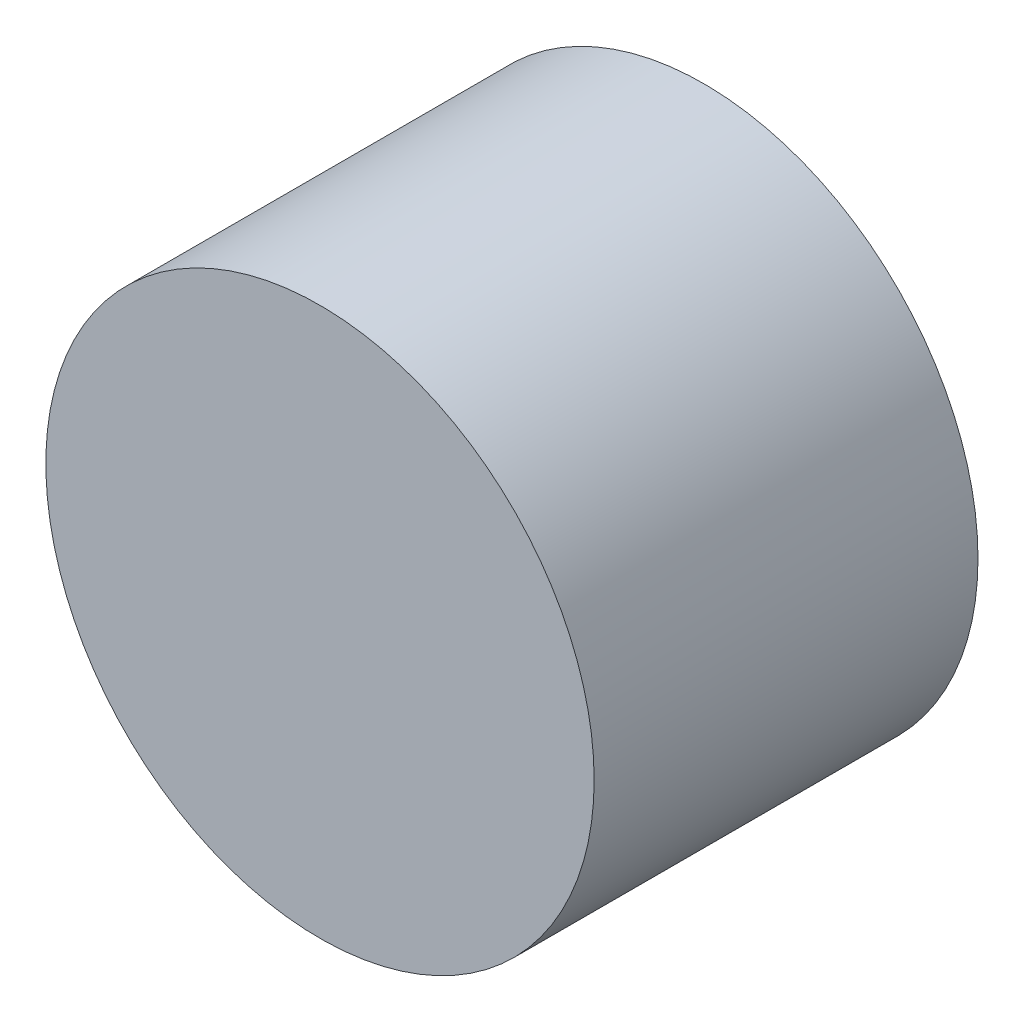
SolidWorks part; units mm, degrees
ref_plane "Front" through (0, 0, 0) normal (0, 0, 1) x (1, 0, 0)
ref_plane "Top" through (0, 0, 0) normal (0, 1, 0) x (1, 0, 0)
ref_plane "Right" through (0, 0, 0) normal (1, 0, 0) x (0, 0, -1)
sketch "Sketch1" plane through (0, 0, 0) normal (0, 0, 1) x (1, 0, 0)
  circle A0 centre (0, 0) radius 6.35
  dimension "D1" = 12.7
extrude "Boss-Extrude1" add sketch "Sketch1" along normal blind 8.89
